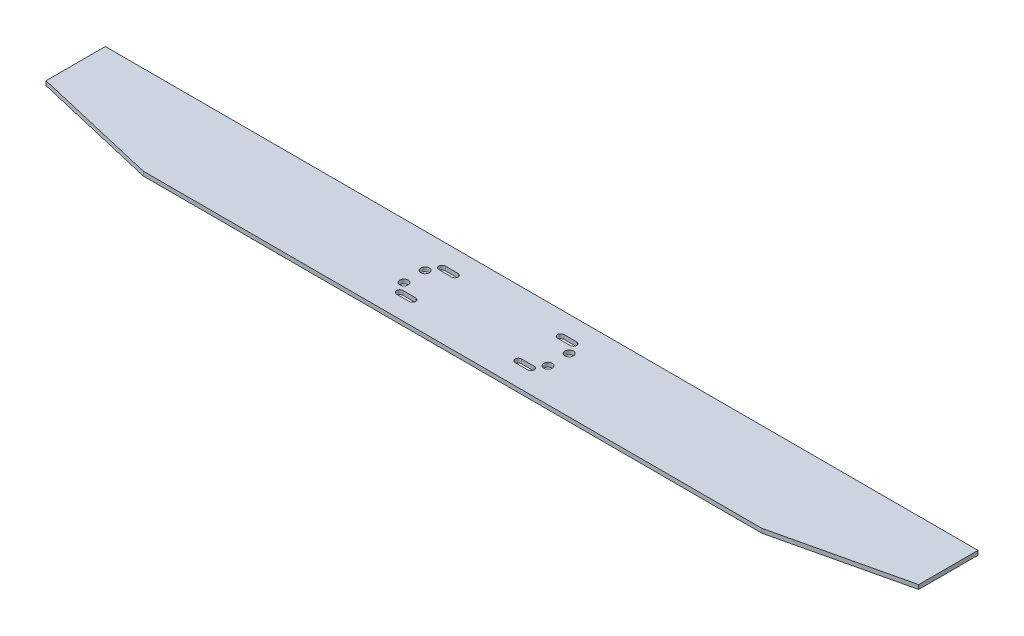
SolidWorks part; units mm, degrees
ref_plane "前视基准面" through (0, 0, 0) normal (0, 0, 1) x (1, 0, 0)
ref_plane "上视基准面" through (0, 0, 0) normal (0, 1, 0) x (1, 0, 0)
ref_plane "右视基准面" through (0, 0, 0) normal (1, 0, 0) x (0, 0, -1)
sketch "草图1" plane through (0, 0, 0) normal (0, 1, 0) x (1, 0, 0)
  line L0 (103, 0) -> (-103, 0)
  line L2 (-73, -21) -> (73, -21)
  line L3 (73, -21) -> (103, -14)
  line L4 (103, -14) -> (103, 0)
  line L5 (-103, 0) -> (-103, -14)
  line L6 (-103, -14) -> (-73, -21)
  point P4 (0, 0)
  dimension "D1" = 21
  dimension "D2" = 206
  dimension "D3" = 14
  dimension "D4" = 30
extrude "凸台-拉伸1" add sketch "草图1" along normal mid plane 1
sketch "草图2" plane through (0, 0.5, 0) normal (0, 1, 0) x (1, 0, 0)
  line L0 (103, -14) -> (103, 0) construction
  line L1 (-16.5, -5.5) -> (11.5, -5.5) construction
  line L2 (-16.5, -5.5) -> (-16.5, -15.5) construction
  line L3 (-16.5, -15.5) -> (11.5, -15.5) construction
  line L4 (11.5, -5.5) -> (11.5, -15.5) construction
  line L5 (-16.5, -5.5) -> (11.5, -15.5) construction
  line L6 (-16.5, -15.5) -> (11.5, -5.5) construction
  line L7 (10, -4.75) -> (13, -4.75)
  line L8 (10, -4.75) -> (10, -6.25)
  line L9 (10, -6.25) -> (13, -6.25)
  line L10 (13, -4.75) -> (13, -6.25)
  line L11 (10, -4.75) -> (13, -6.25) construction
  line L12 (10, -6.25) -> (13, -4.75) construction
  line L13 (103, 0) -> (-103, 0) construction
  line L14 (-2.5, -15.5) -> (-2.5, -5.5) construction
  line L15 (10, -14.75) -> (13, -14.75)
  line L16 (10, -14.75) -> (10, -16.25)
  line L17 (10, -16.25) -> (13, -16.25)
  line L18 (13, -14.75) -> (13, -16.25)
  line L19 (10, -14.75) -> (13, -16.25) construction
  line L20 (10, -16.25) -> (13, -14.75) construction
  line L21 (-18, -14.75) -> (-15, -14.75)
  line L22 (-18, -14.75) -> (-18, -16.25)
  line L23 (-18, -16.25) -> (-15, -16.25)
  line L24 (-15, -14.75) -> (-15, -16.25)
  line L25 (-18, -14.75) -> (-15, -16.25) construction
  line L26 (-18, -16.25) -> (-15, -14.75) construction
  line L27 (-18, -4.75) -> (-15, -4.75)
  line L28 (-18, -4.75) -> (-18, -6.25)
  line L29 (-18, -6.25) -> (-15, -6.25)
  line L30 (-15, -4.75) -> (-15, -6.25)
  line L31 (-18, -4.75) -> (-15, -6.25) construction
  line L32 (-18, -6.25) -> (-15, -4.75) construction
  line L33 (14.5, -13) -> (14.5, -8) construction
  circle A0 centre (14.5, -13) radius 1
  circle A1 centre (14.5, -8) radius 1
  circle A2 centre (-19.5, -8) radius 1
  circle A3 centre (-19.5, -13) radius 1
  point P0 (-2.5, -10.5)
  point P31 (14.5, -10.5)
  dimension "D7" = 2
  dimension "D8" = 5
  dimension "D1" = 90
  dimension "D2" = 4.75
  dimension "D3" = 3
  dimension "D4" = 1.5
  dimension "D5" = 25
  dimension "D6" = 8.5
  dimension "D9" = 1.5
extrude "切除-拉伸1" cut sketch "草图2" against normal through all
sketch "草图3" plane through (0, 0.5, 0) normal (0, 1, 0) x (1, 0, 0)
  line L1 (-18, -4.75) -> (-18, -6.25) construction
  line L2 (-15, -6.25) -> (-15, -4.75) construction
  line L3 (-18, -14.75) -> (-18, -16.25) construction
  line L4 (-15, -16.25) -> (-15, -14.75) construction
  line L5 (10, -4.75) -> (10, -6.25) construction
  line L6 (10, -14.75) -> (10, -16.25) construction
  line L7 (13, -16.25) -> (13, -14.75) construction
  line L8 (13, -6.25) -> (13, -4.75) construction
  circle A5 centre (-18, -5.5) radius 0.75
  circle A6 centre (-15, -5.5) radius 0.75
  circle A7 centre (-18, -15.5) radius 0.75
  circle A8 centre (-15, -15.5) radius 0.75
  circle A9 centre (10, -5.5) radius 0.75
  circle A10 centre (10, -15.5) radius 0.75
  circle A11 centre (13, -15.5) radius 0.75
  circle A12 centre (13, -5.5) radius 0.75
extrude "切除-拉伸2" cut sketch "草图3" against normal through all
